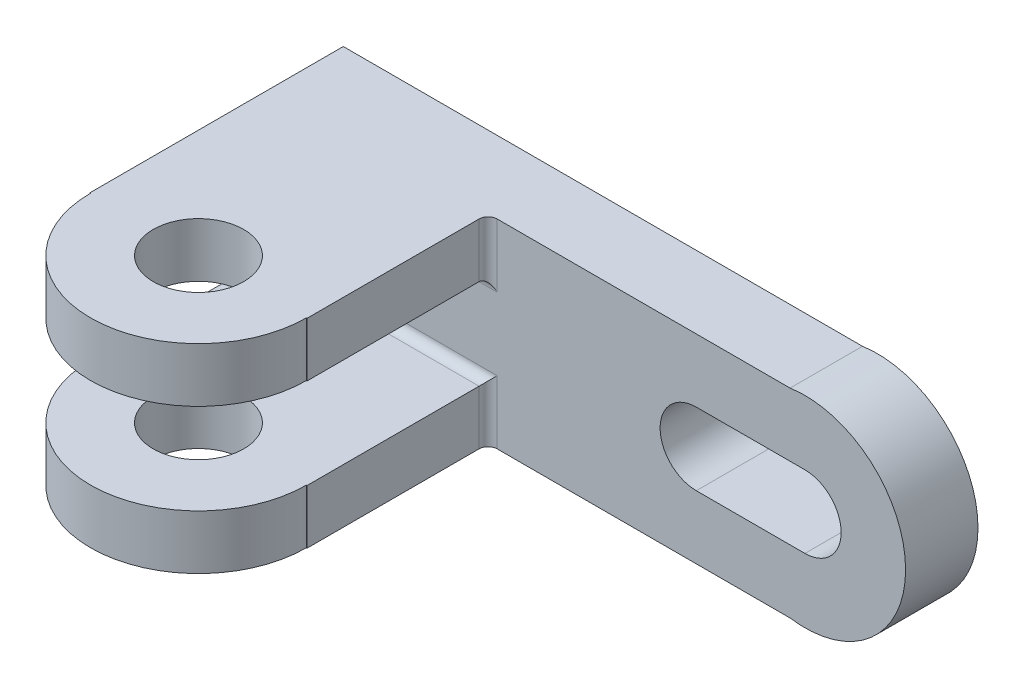
SolidWorks part; units mm, degrees
ref_plane "Front Plane" through (0, 0, 0) normal (0, 0, 1) x (1, 0, 0)
ref_plane "Top Plane" through (0, 0, 0) normal (0, 1, 0) x (1, 0, 0)
ref_plane "Right Plane" through (0, 0, 0) normal (1, 0, 0) x (0, 0, -1)
sketch "Sketch1" plane through (0, 0, 0) normal (0, 0, 1) x (1, 0, 0)
  line L1 (-41.923, -26.2385) -> (76.077, -26.2385)
  line L2 (-41.923, -26.2385) -> (-41.923, 17.7615)
  line L3 (-41.923, 17.7615) -> (76.077, 17.7615)
  line L4 (76.077, -26.2385) -> (76.077, 17.7615)
  dimension "D1" = 118
  dimension "D2" = 44
extrude "Boss-Extrude1" add sketch "Sketch1" along normal blind 16
sketch "Sketch2" plane through (0, 0, 16) normal (0, 0, 1) x (1, 0, 0)
  line L0 (76.077, -26.2385) -> (76.077, 17.7615) construction
  circle A0 centre (76.077, -4.2385) radius 22.2425
extrude "Boss-Extrude2" add sketch "Sketch2" against normal blind 16
sketch "Sketch3" plane through (0, 0, 16) normal (0, 0, 1) x (1, 0, 0)
  line L0 (76.077, -4.2385) -> (52.077, -4.2385) construction
  line L1 (76.077, -12.2385) -> (52.077, -12.2385)
  line L2 (76.077, 3.7615) -> (52.077, 3.7615)
  arc A0 (76.077, -12.2385) -> (76.077, 3.7615) centre (76.077, -4.2385) ccw
  arc A1 (52.077, 3.7615) -> (52.077, -12.2385) centre (52.077, -4.2385) ccw
  point P3 (64.077, -4.2385)
  dimension "D1" = 16
  dimension "D2" = 24
extrude "Cut-Extrude1" cut sketch "Sketch3" against normal through all contours L2 A1 L1 A0
sketch "Sketch4" plane through (0, -26.2385, 0) normal (0, -1, 0) x (1, 0, 0)
  line L5 (-41.923, 16) -> (-41.923, 56)
  line L10 (-41.923, 56) -> (-41.7742, 56)
  line L11 (6.077, 56) -> (6.077, 16)
  line L12 (-41.923, 16) -> (72.8015, 16) construction
  line L13 (6.077, 16) -> (-41.923, 16)
  line L14 (5.9283, 56) -> (6.077, 56)
  arc A1 (5.9283, 56) -> (-41.7742, 56) centre (-17.923, 56) ccw
  circle A2 centre (-17.923, 56) radius 10
  dimension "D3" = 20
  dimension "D1" = 40
  dimension "D2" = 48
extrude "Boss-Extrude9" add sketch "Sketch4" against normal blind 12 contours A1 L10 L5 L13 L11 L14 | A2
ref_plane "Plane8" through (0, -4.2385, 0) normal (0, 1, 0) x (1, 0, 0)
mirror "Mirror14" about plane through (0, -4.2385, 0) normal (0, 1, 0) of "Boss-Extrude9"
fillet "Fillet1" radius 2 4 edges at (-17.923, -14.2385, 16) (-17.923, 5.7615, 16) (6.077, 11.7615, 16) (6.077, -20.2385, 16)
